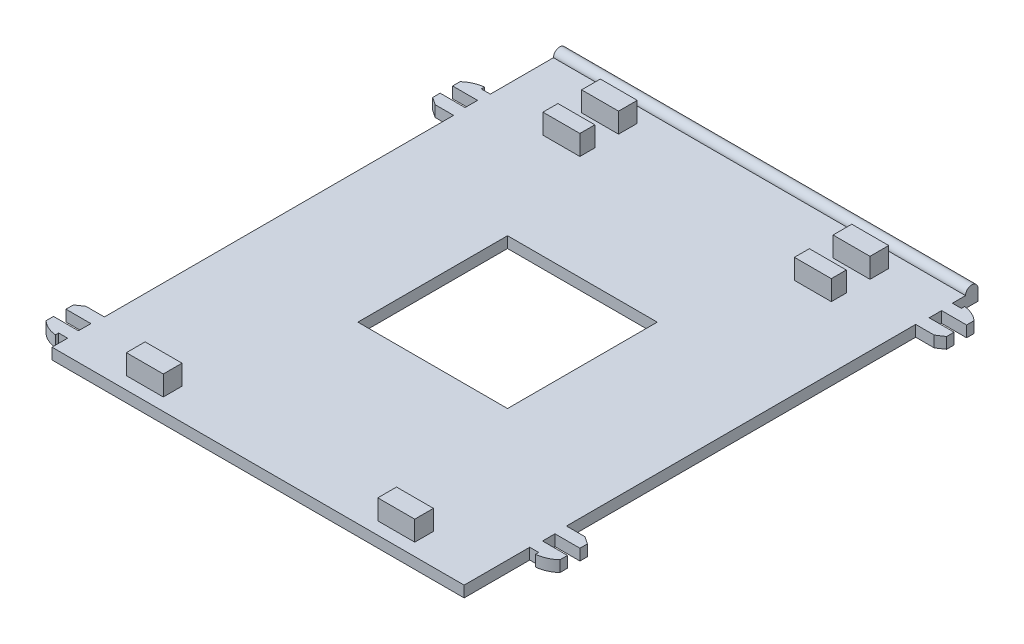
SolidWorks part; units mm, degrees
ref_plane "Front" through (0, 0, 0) normal (0, 0, 1) x (1, 0, 0)
ref_plane "Top" through (0, 0, 0) normal (0, 1, 0) x (1, 0, 0)
ref_plane "Right" through (0, 0, 0) normal (1, 0, 0) x (0, 0, -1)
sketch "Sketch1" plane through (0, 0, 0) normal (0, 1, 0) x (1, 0, 0)
  line L0 (43.1, 45.51) -> (46.5, 45.51)
  line L1 (-41.3, 50) -> (41.3, 50)
  line L2 (-41.3, 50) -> (-41.3, -50)
  line L3 (-41.3, -50) -> (41.3, -50)
  line L4 (41.3, 50) -> (41.3, -50)
  line L5 (-41.3, 50) -> (41.3, -50) construction
  line L6 (-41.3, -50) -> (41.3, 50) construction
  line L7 (41.3, 47.87) -> (43.1, 47.87)
  line L8 (41.3, 47.87) -> (41.3, 45.51)
  line L9 (41.3, 45.51) -> (43.1, 45.51)
  line L10 (43.1, 47.87) -> (43.1, 45.51)
  line L11 (46.5, 45.51) -> (46.5, 47.01)
  line L12 (43.1, 47.87) -> (43.1, 48.52)
  line L13 (41.3, 45.51) -> (41.5, 45.51)
  line L14 (41.3, 45.51) -> (41.3, 43.01)
  line L15 (41.3, 43.01) -> (41.5, 43.01)
  line L16 (41.5, 45.51) -> (41.5, 43.01)
  line L17 (41.5, 43.01) -> (46.5, 43.01)
  line L18 (46.5, 43.01) -> (46.5, 41.51)
  line L19 (46.5, 41.51) -> (45, 40.51)
  line L20 (45, 40.51) -> (41.3, 40.51)
  line L21 (41.3, 5.51) -> (60.4529, 5.51) construction
  line L22 (41.5, -31.99) -> (46.5, -31.99)
  line L23 (46.5, -31.99) -> (46.5, -30.49)
  line L24 (46.5, -30.49) -> (45, -29.49)
  line L25 (45, -29.49) -> (41.3, -29.49)
  line L26 (43.1, -36.85) -> (43.1, -37.5)
  line L27 (46.5, -34.49) -> (46.5, -35.99)
  line L28 (43.1, -34.49) -> (46.5, -34.49)
  line L29 (41.3, -34.49) -> (43.1, -34.49)
  line L30 (43.1, -36.85) -> (43.1, -34.49)
  line L31 (41.3, -36.85) -> (43.1, -36.85)
  line L32 (41.3, -36.85) -> (41.3, -34.49)
  line L33 (41.3, -31.99) -> (41.5, -31.99)
  line L34 (41.5, -34.49) -> (41.5, -31.99)
  line L35 (41.3, -34.49) -> (41.5, -34.49)
  line L36 (41.3, -34.49) -> (41.3, -31.99)
  line L37 (0, 36.7793) -> (0, -23.6766) construction
  line L38 (-41.3, -4.51) -> (-64.7336, -4.51) construction
  line L39 (-45, -39.51) -> (-41.3, -39.51)
  line L40 (-46.5, -40.51) -> (-45, -39.51)
  line L41 (-46.5, -42.01) -> (-46.5, -40.51)
  line L42 (-41.5, -42.01) -> (-46.5, -42.01)
  line L43 (-41.5, -44.51) -> (-41.5, -42.01)
  line L44 (-41.3, -44.51) -> (-46.5, -44.51)
  line L45 (-43.1, -46.87) -> (-41.3, -46.87)
  line L46 (-43.1, -46.87) -> (-43.1, -47.52)
  line L47 (-46.5, -44.51) -> (-46.5, -46.01)
  line L59 (-41.3, 47.87) -> (-41.3, 45.51)
  line L60 (-41.3, 47.87) -> (-41.3, 37.87) construction
  line L61 (-43.1, 37.85) -> (-41.3, 37.85)
  line L62 (-43.1, 37.85) -> (-43.1, 38.5)
  line L63 (-41.3, 35.49) -> (-46.5, 35.49)
  line L64 (-46.5, 35.49) -> (-46.5, 36.99)
  line L65 (-41.5, 35.49) -> (-41.5, 32.99)
  line L66 (-41.5, 32.99) -> (-46.5, 32.99)
  line L67 (-46.5, 32.99) -> (-46.5, 31.49)
  line L68 (-46.5, 31.49) -> (-45, 30.49)
  line L69 (-45, 30.49) -> (-41.3, 30.49)
  arc A0 (43.1, 48.52) -> (46.5, 47.01) centre (42.5287, 42.6507) cw
  arc A1 (43.1, -37.5) -> (46.5, -35.99) centre (42.5287, -31.6307) ccw
  arc A2 (-46.5, -46.01) -> (-43.1, -47.52) centre (-42.5287, -41.6507) ccw
  arc A4 (-46.5, 36.99) -> (-43.1, 38.5) centre (-42.5287, 32.6307) cw
  point P0 (0, 0)
  dimension "D9" = 0.65
  dimension "D10" = 5.897
  dimension "D25" = 5.897
  dimension "D1" = 82.6
  dimension "D2" = 100
  dimension "D3" = 2.13
  dimension "D4" = 2.36
  dimension "D5" = 1.8
  dimension "D6" = 0.2
  dimension "D7" = 5.2
  dimension "D8" = 1.5
  dimension "D11" = 2.5
  dimension "D12" = 1.5
  dimension "D13" = 3.7
  dimension "D14" = 2.5
  dimension "D15" = 5.2
  dimension "D16" = 35
  dimension "D17" = 10
  dimension "D18" = 5.2
  dimension "D19" = 1.8
  dimension "D20" = 1.5
  dimension "D21" = 12.15
  dimension "D22" = 2.36
  dimension "D23" = 0.2
  dimension "D24" = 0.65
  dimension "D26" = 1.5
  dimension "D27" = 2.5
  dimension "D28" = 3.7
  dimension "D29" = 5
  dimension "D30" = 2.5
  dimension "D31" = 35
  dimension "D32" = 3.13
extrude "Boss-Extrude1" add sketch "Sketch1" along normal blind 2.23 contours L26 A1 L27 L28 L30 | L4 L31 L30 L29 | L4 L33 L22 L23 L24 L25 | L29 L34 L33 L4 | L4 L1 L2 L3 | L20 L19 L18 L17 L15 L4 | L16 L9 L4 L15 | L10 L7 L4 L9 | A0 L12 L10 L0 L11 | L47 A2 L46 L45 L2 L44 | L44 L2 L39 L40 L41 L42 L43 | L68 L69 L2 L63 L65 L66 L67 | A4 L64 L63 L2 L61 L62
sketch "Sketch2" plane through (0, 2.23, 0) normal (0, 1, 0) x (1, 0, 0)
  line L0 (-41.3, -50) -> (41.3, -50) construction
  line L1 (-21.5, -43.75) -> (-28.9, -43.75)
  line L2 (-21.5, -43.75) -> (-21.5, -47.5)
  line L3 (-21.5, -47.5) -> (-28.9, -47.5)
  line L4 (-28.9, -43.75) -> (-28.9, -47.5)
  line L5 (-41.5, -44.51) -> (-41.5, -42.01) construction
  line L6 (0, -50) -> (0, -10.7982) construction
  line L7 (21.5, -43.75) -> (21.5, -47.5)
  line L8 (21.5, -47.5) -> (28.9, -47.5)
  line L9 (28.9, -43.75) -> (28.9, -47.5)
  line L10 (21.5, -43.75) -> (28.9, -43.75)
  line L11 (-26.6786, 0) -> (25.6107, 0) construction
  line L12 (21.5, 47.5) -> (28.9, 47.5)
  line L13 (28.9, 43.75) -> (28.9, 47.5)
  line L14 (21.5, 43.75) -> (28.9, 43.75)
  line L15 (21.5, 43.75) -> (21.5, 47.5)
  line L16 (-21.5, 43.75) -> (-21.5, 47.5)
  line L17 (-21.5, 47.5) -> (-28.9, 47.5)
  line L18 (-28.9, 43.75) -> (-28.9, 47.5)
  line L19 (-21.5, 43.75) -> (-28.9, 43.75)
  line L20 (-28.9, 36) -> (-28.9, 39)
  line L21 (-28.9, -36) -> (-21.5, -36)
  line L22 (-28.9, -36) -> (-28.9, -39)
  line L23 (-28.9, -39) -> (-21.5, -39)
  line L24 (-21.5, -36) -> (-21.5, -39)
  line L25 (-28.9, 36) -> (-21.5, 36)
  line L26 (-21.5, 36) -> (-21.5, 39)
  line L27 (-28.9, 39) -> (-21.5, 39)
  line L28 (28.9, 36) -> (28.9, 39)
  line L29 (28.9, 36) -> (21.5, 36)
  line L30 (21.5, 36) -> (21.5, 39)
  line L31 (28.9, 39) -> (21.5, 39)
  line L32 (21.5, -36) -> (21.5, -39)
  line L33 (28.9, -36) -> (21.5, -36)
  line L34 (28.9, -36) -> (28.9, -39)
  line L35 (28.9, -39) -> (21.5, -39)
  dimension "D1" = 2.5
  dimension "D2" = 12.6
  dimension "D3" = 7.4
  dimension "D4" = 3.75
  dimension "D5" = 4.75
  dimension "D6" = 3
  dimension "D7" = 7.4
extrude "Boss-Extrude2" add sketch "Sketch2" along normal blind 4 contours L2 L1 L4 L3 | L7 L8 L9 L10 | L16 L17 L18 L19 | L20 L27 L26 L25 | L28 L31 L30 L29 | L12 L13 L14 L15
sketch "Sketch3" plane through (0, 2.23, 0) normal (0, 1, 0) x (1, 0, 0)
  line L1 (-15, 15) -> (15, 15)
  line L2 (-15, 15) -> (-15, -15)
  line L3 (-15, -15) -> (15, -15)
  line L4 (15, 15) -> (15, -15)
  line L5 (-15, 15) -> (15, -15) construction
  line L6 (-15, -15) -> (15, 15) construction
  point P0 (0, 0)
  dimension "D1" = 30
  dimension "D2" = 30
extrude "Cut-Extrude1" cut sketch "Sketch3" against normal blind 10
sketch "Sketch4" plane through (-41.3, 0, 0) normal (-1, 0, 0) x (0, 0, 1)
  line L0 (-50, 0) -> (-53, 0)
  line L1 (-50, 2.23) -> (-53, 2.23)
  line L2 (-53, 2.23) -> (-53, 0)
  arc A1 (-53, 2.23) -> (-50.5, 2.23) centre (-51.75, 2.23) cw
  dimension "D2" = 1.25
  dimension "D1" = 3
extrude "Boss-Extrude3" add sketch "Sketch4" against normal up to vertex
sketch "Sketch5" plane through (0, 0, 0) normal (0, -1, 0) x (1, 0, 0)
  line L0 (41.3, -40) -> (-41.3, -40) construction
  line L1 (41.3, -40.51) -> (41.3, 29.49) construction
  line L2 (-41.3, -30.49) -> (-41.3, 39.51) construction
  line L3 (41.3, -53) -> (-41.3, -53) construction
  text T0 "+Z↑"
  dimension "D1" = 13
extrude "Cut-Extrude2" cut sketch "Sketch5" against normal blind 0.5
